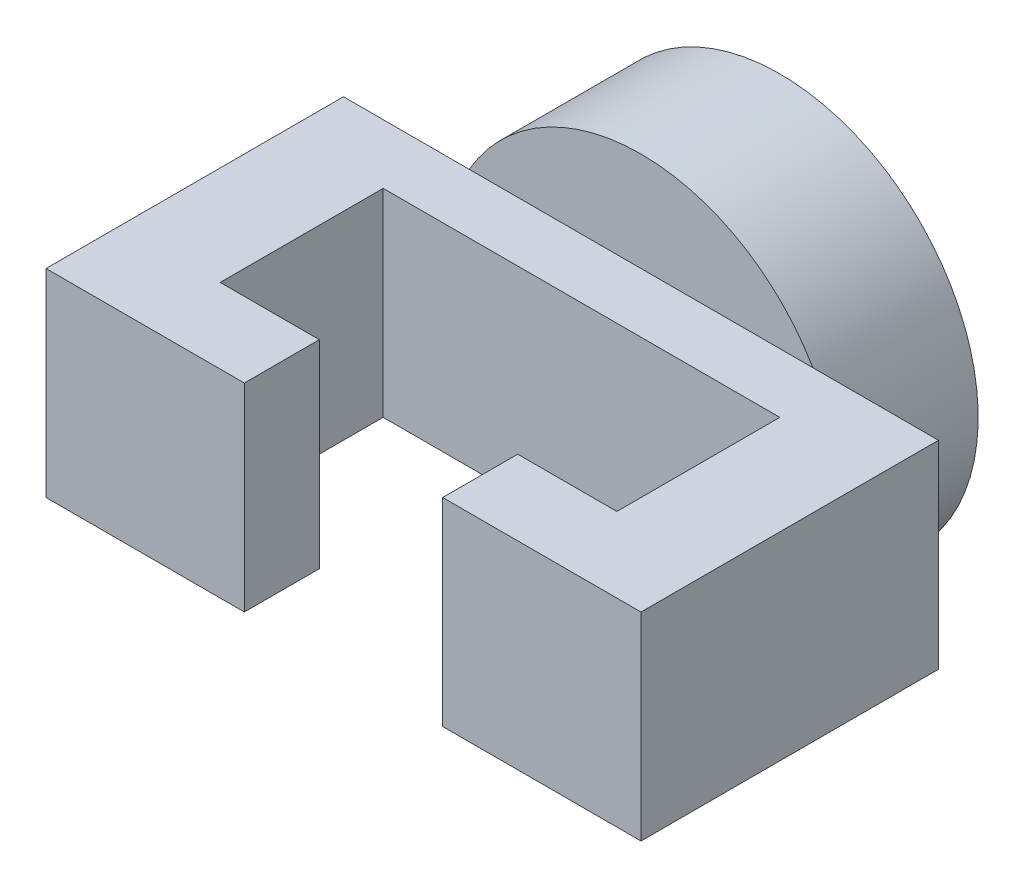
SolidWorks part; units mm, degrees
ref_plane "Alzado" through (0, 0, 0) normal (0, 0, 1) x (1, 0, 0)
ref_plane "Planta" through (0, 0, 0) normal (0, 1, 0) x (1, 0, 0)
ref_plane "Vista lateral" through (0, 0, 0) normal (1, 0, 0) x (0, 0, -1)
sketch "Croquis1" plane through (0, 0, 0) normal (0, 0, 1) x (1, 0, 0)
  circle A0 centre (0, 0) radius 100
  dimension "D1" = 200
extrude "Saliente-Extruir1" add sketch "Croquis1" along normal blind 50
sketch "Croquis2" plane through (0, 0, 50) normal (0, 0, 1) x (1, 0, 0)
  line L0 (150, -50) -> (-150, -50)
  line L1 (150, -50) -> (150, 50)
  line L2 (-150, -50) -> (-150, 50)
  line L3 (150, 50) -> (-150, 50)
  line L4 (150, -50) -> (-150, 50) construction
  line L5 (-150, -50) -> (150, 50) construction
  point P1 (0, 0)
  dimension "D1" = 100
  dimension "D2" = 300
extrude "Saliente-Extruir2" add sketch "Croquis2" along normal blind 150
sketch "Croquis3" plane through (0, -50, 0) normal (0, -1, 0) x (1, 0, 0)
  line L0 (-150, 200) -> (-150, 50) construction
  line L1 (-100, 162.1704) -> (-50, 162.1704)
  line L2 (-100, 162.1704) -> (-100, 80)
  line L3 (-100, 80) -> (100, 80)
  line L4 (100, 162.1704) -> (100, 80)
  line L5 (150, 200) -> (150, 50) construction
  line L6 (-86.6025, 50) -> (86.6025, 50) construction
  line L7 (-150, 200) -> (150, 200) construction
  line L8 (-50, 200) -> (50, 200)
  line L9 (-50, 200) -> (-50, 162.1704)
  line L11 (50, 200) -> (50, 162.1704)
  line L12 (50, 162.1704) -> (100, 162.1704)
  dimension "D1" = 50
  dimension "D2" = 50
  dimension "D3" = 30
  dimension "D4" = 100
  dimension "D5" = 100
extrude "Cortar-Extruir1" cut sketch "Croquis3" against normal blind 150
sketch "Croquis4" plane through (0, 0, 0) normal (0, 1, 0) x (1, 0, 0)
  line L0 (0, 0) -> (0, -227.4133) construction
  line L1 (0, -181.0852) -> (77.2202, -181.0852) construction
  line L2 (100, -162.1704) -> (50, -162.1704) construction
  line L3 (150, -200) -> (50, -200) construction
sketch "Croquis5" plane through (0, 0, 0) normal (0, 0, -1) x (-1, 0, 0)
  line L0 (0, 48.6487) -> (0, -45.8688) construction
sketch "Croquis6" plane through (0, 0, 0) normal (0, 0, -1) x (-1, 0, 0)
  circle A0 centre (0, 0) radius 100
extrude "Saliente-Extruir3" add sketch "Croquis6" along normal blind 20
